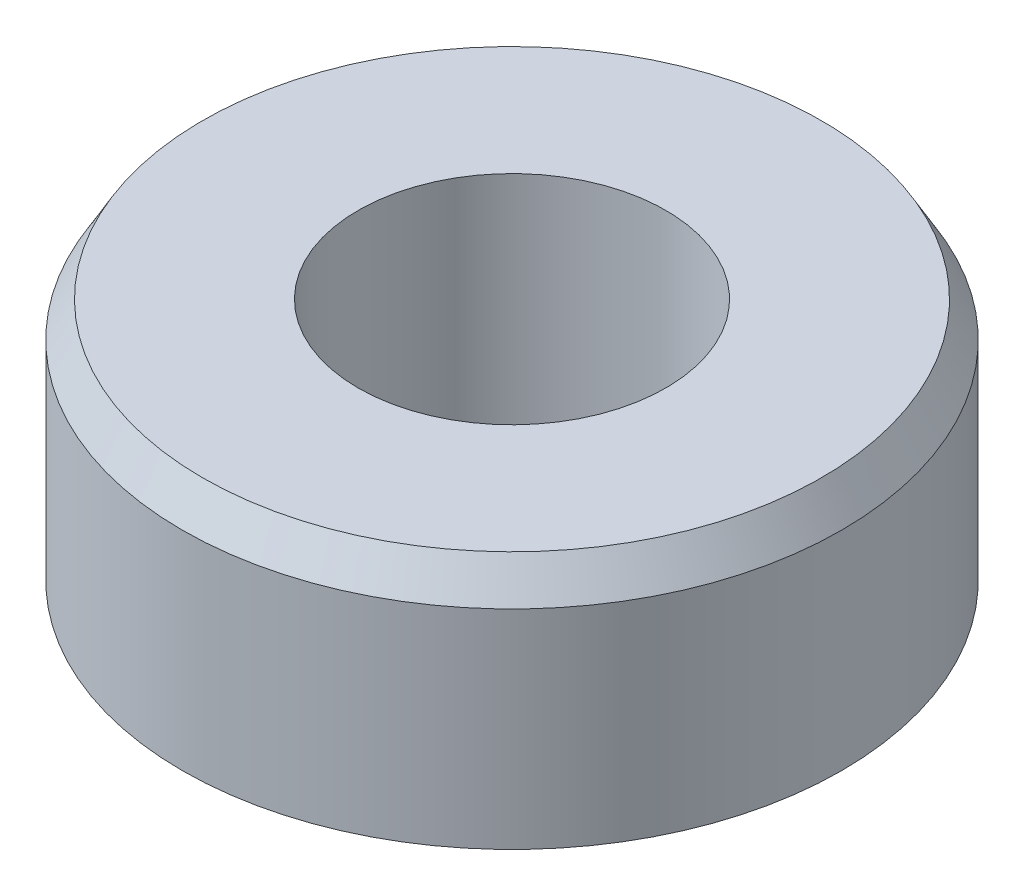
SolidWorks part; units mm, degrees
ref_plane "Front Plane" through (0, 0, 0) normal (0, 0, 1) x (1, 0, 0)
ref_plane "Top Plane" through (0, 0, 0) normal (0, 1, 0) x (1, 0, 0)
ref_plane "Right Plane" through (0, 0, 0) normal (1, 0, 0) x (0, 0, -1)
sketch "Sketch1" plane through (0, 0, 0) normal (0, 1, 0) x (1, 0, 0)
  circle A0 centre (0, 0) radius 3.75
  circle A1 centre (0, 0) radius 1.75
  dimension "D1" = 3.5
  dimension "D2" = 7.5
extrude "Boss-Extrude1" add sketch "Sketch1" along normal blind 3
chamfer "Chamfer1" distance 0.4 angle 30 2 edges at (0, 0, 3.75) (0, 3, 3.75)
